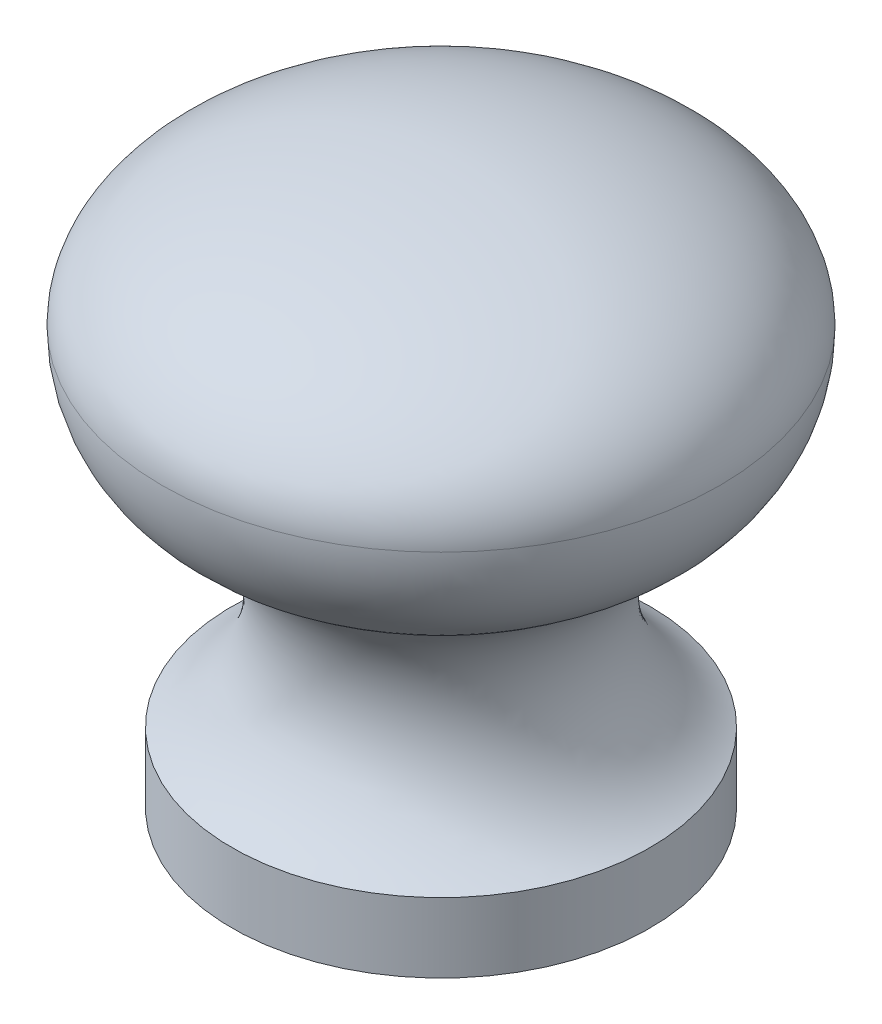
SolidWorks part; units mm, degrees
material "PW40:15:Sc:0:Re:24:"
ref_plane "Front" through (0, 0, 0) normal (0, 0, 1) x (1, 0, 0)
ref_plane "Top" through (0, 0, 0) normal (0, 1, 0) x (1, 0, 0)
ref_plane "Right" through (0, 0, 0) normal (1, 0, 0) x (0, 0, -1)
sketch "Sketch1" plane through (0, 0, 0) normal (0, 0, 1) x (1, 0, 0)
  line L0 (0, 0) -> (0, 44.9854) construction
  line L1 (0, 0) -> (-9.525, 0)
  line L2 (-9.525, 0) -> (-9.525, 3.175)
  line L3 (0, 25.4) -> (0, 0)
  arc A0 (-9.525, 3.175) -> (-9.3873, 13.4735) centre (-12.1722, 8.3606) ccw
  arc A1 (-12.7, 19.05) -> (-9.3873, 13.4735) centre (-6.35, 19.05) ccw
  ellipse E0 centre (0, 19.05) end of major axis (-12.7, 19.05) minor radius 6.35 (0, 25.4) -> (-12.7, 19.05) ccw
  dimension "D1" = 6.35
  dimension "D2" = 25.4
  dimension "D3" = 25.4
  dimension "D7" = 6.35
  dimension "D8" = 5.8222
  dimension "D4" = 19.05
  dimension "D5" = 3.175
revolve "Base-Revolve" add sketch "Sketch1" angle 360 about L0
hole_wizard "#8-32 Tapped Hole1" positions "Sketch3" profile "Sketch2" tap size "#8-32" standard "Ansi Inch"
sketch "Sketch3" plane through (0, 0, 0) normal (0, -1, 0) x (1, 0, 0)
  circle A0 centre (0, 0) radius 9.525 construction
  point P0 (0, 0)
sketch "Sketch2" plane through (0, 0, 0) normal (1, 0, 0) x (0, 0, -1)
  line L0 (0, 0) -> (0, 16.1152)
  line L1 (0, 16.1152) -> (1.7272, 15.0774)
  line L2 (1.7272, 15.0774) -> (1.7272, 12.7)
  line L3 (1.7272, 12.7) -> (2.0828, 12.7)
  line L4 (2.0828, 12.7) -> (2.0828, 0)
  line L5 (2.0828, 0) -> (0, 0)
  line L10 (0, 16.1152) -> (-1.7272, 15.0774) construction
  line L11 (0, -6.35) -> (0, 107.95) construction
  dimension "Tap Drill Dia." = 3.4544
  dimension "Tap Drill Depth" = 15.0774
  dimension "Thread Dia." = 4.1656
  dimension "Thread Depth" = 12.7
  dimension "Drill Angle" = 118
